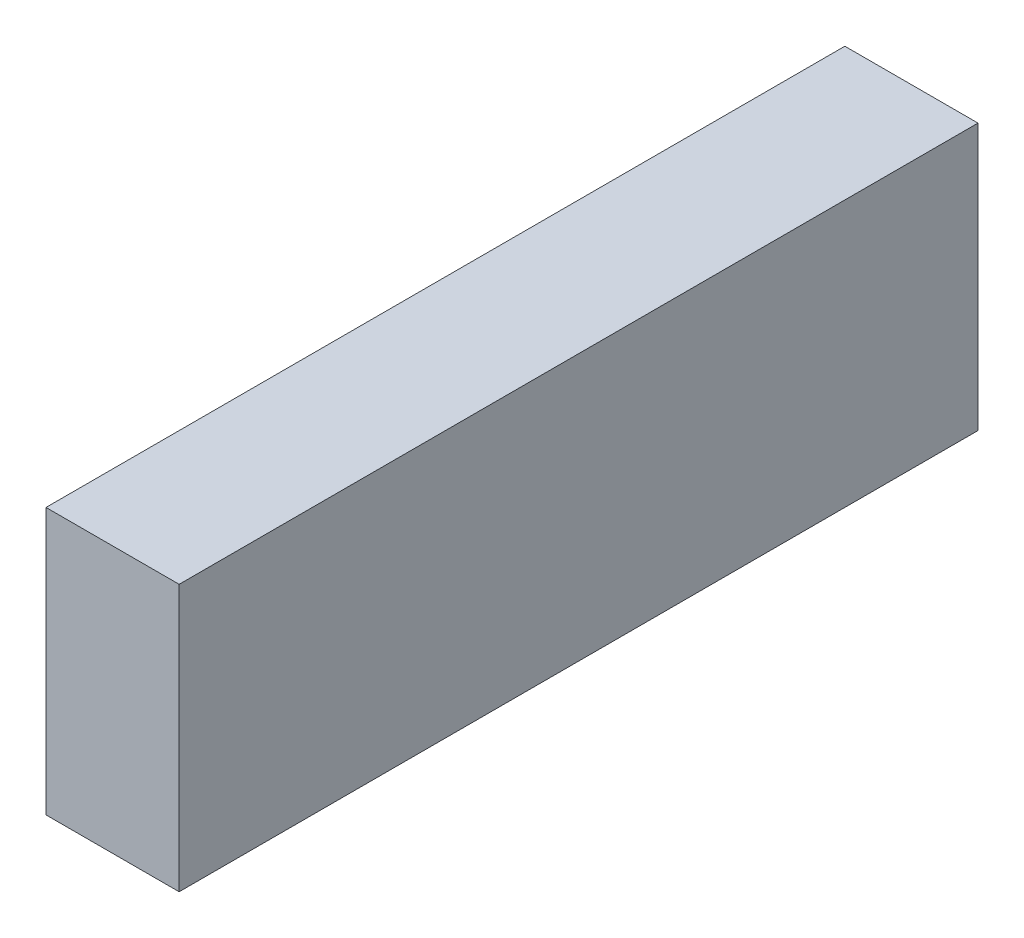
SolidWorks part; units mm, degrees
ref_plane "Front" through (0, 0, 0) normal (0, 0, 1) x (1, 0, 0)
ref_plane "Top" through (0, 0, 0) normal (0, 1, 0) x (1, 0, 0)
ref_plane "Right" through (0, 0, 0) normal (1, 0, 0) x (0, 0, -1)
sketch "草图1" plane through (0, 0, 0) normal (0, 1, 0) x (1, 0, 0)
  line L1 (-25, -150) -> (25, -150)
  line L2 (-25, -150) -> (-25, 150)
  line L3 (-25, 150) -> (25, 150)
  line L4 (25, -150) -> (25, 150)
  line L5 (-25, -150) -> (25, 150) construction
  line L6 (-25, 150) -> (25, -150) construction
  point P0 (0, 0)
  dimension "D1" = 50
  dimension "D2" = 300
extrude "凸台-拉伸1" add sketch "草图1" along normal blind 100
